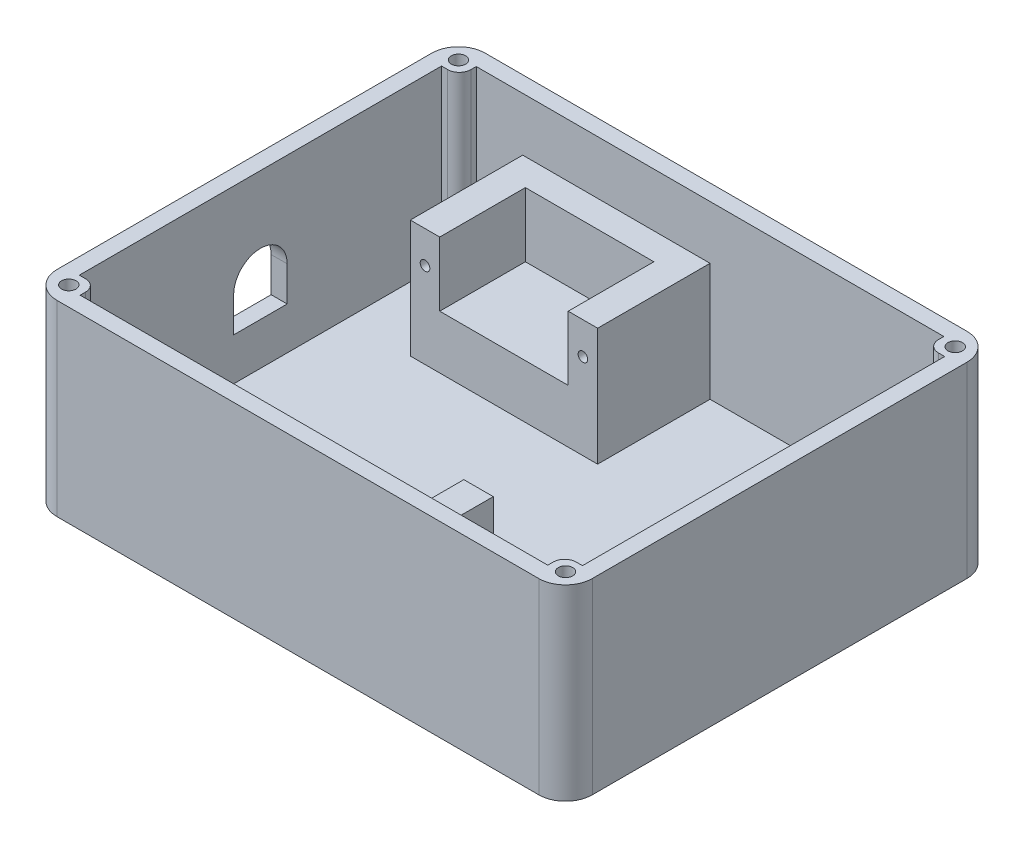
SolidWorks part; units mm, degrees
ref_plane "Front" through (0, 0, 0) normal (0, 0, 1) x (1, 0, 0)
ref_plane "Top" through (0, 0, 0) normal (0, 1, 0) x (1, 0, 0)
ref_plane "Right" through (0, 0, 0) normal (1, 0, 0) x (0, 0, -1)
sketch "草图1" plane through (0, 0, 0) normal (0, 1, 0) x (1, 0, 0)
  line L1 (-45, 40) -> (45, 40)
  line L2 (-50, 35) -> (-50, -35)
  line L3 (-45, -40) -> (45, -40)
  line L4 (50, 35) -> (50, -35)
  line L5 (-50, 40) -> (50, -40) construction
  line L6 (-50, -40) -> (50, 40) construction
  arc A0 (-50, -35) -> (-45, -40) centre (-45, -35) ccw
  arc A1 (45, -40) -> (50, -35) centre (45, -35) ccw
  arc A2 (45, 40) -> (50, 35) centre (45, 35) cw
  arc A3 (-45, 40) -> (-50, 35) centre (-45, 35) ccw
  point P0 (0, 0)
  dimension "D3" = 5
  dimension "D1" = 100
  dimension "D2" = 80
extrude "凸台-拉伸1" add sketch "草图1" along normal blind 35
shell "抽壳2" thickness 3
sketch "草图2" plane through (0, 3, 0) normal (0, 1, 0) x (1, 0, 0)
  line L0 (0, 15.372) -> (0, -17.8847) construction
  line L2 (45, 37) -> (-45, 37) construction
  line L3 (-18.0497, 0) -> (18.0623, 0) construction
  line L4 (47, 33.835) -> (47, 35)
  line L5 (45.8439, 33.835) -> (47, 33.835)
  line L6 (43.6788, 36) -> (43.6788, 37)
  line L7 (-43.6788, 36) -> (-43.6788, 37)
  line L8 (-45.8439, 33.835) -> (-47, 33.835)
  line L9 (-47, 35) -> (-47, -35) construction
  line L10 (-47, 33.835) -> (-47, 35)
  line L11 (-43.6788, 37) -> (-45, 37)
  line L12 (43.6788, 37) -> (45, 37)
  line L13 (43.6788, -37) -> (45, -37)
  line L14 (43.6788, -36) -> (43.6788, -37)
  line L15 (45.8439, -33.835) -> (47, -33.835)
  line L16 (47, -33.835) -> (47, -35)
  line L17 (-47, -33.835) -> (-47, -35)
  line L18 (-45.8439, -33.835) -> (-47, -33.835)
  line L19 (-43.6788, -36) -> (-43.6788, -37)
  line L20 (-43.6788, -37) -> (-45, -37)
  arc A0 (-45.8439, 33.835) -> (-43.6788, 36) centre (-45.8439, 36) ccw
  arc A1 (-45, 37) -> (-47, 35) centre (-45, 35) ccw construction
  arc A2 (-45, 37) -> (-47, 35) centre (-45, 35) ccw
  arc A3 (45, 37) -> (47, 35) centre (45, 35) cw
  arc A4 (45.8439, 33.835) -> (43.6788, 36) centre (45.8439, 36) cw
  arc A5 (45.8439, -33.835) -> (43.6788, -36) centre (45.8439, -36) ccw
  arc A6 (45, -37) -> (47, -35) centre (45, -35) ccw
  arc A7 (-45, -37) -> (-47, -35) centre (-45, -35) cw
  arc A8 (-45.8439, -33.835) -> (-43.6788, -36) centre (-45.8439, -36) cw
  dimension "D1" = 1
extrude "凸台-拉伸3" add sketch "草图2" along normal blind 32
sketch "草图3" plane through (0, 35, 0) normal (0, 1, 0) x (1, 0, 0)
  line L0 (43.6788, 37) -> (-43.6788, 37) construction
  line L1 (-47, 33.835) -> (-47, -33.835) construction
  line L2 (0, 14.6286) -> (0, -16.7471) construction
  line L3 (-18.4739, 0) -> (20.7457, 0) construction
  circle A0 centre (-46.4, 36.4) radius 1.35
  circle A1 centre (46.4, 36.4) radius 1.35
  circle A2 centre (46.4, -36.4) radius 1.35
  circle A3 centre (-46.4, -36.4) radius 1.35
  dimension "D1" = 0.6
  dimension "D3" = 2.7
  dimension "D2" = 0.6
extrude "切除-拉伸1" cut sketch "草图3" against normal blind 4
sketch "草图6" plane through (-50, 0, 0) normal (-1, 0, 0) x (0, 0, 1)
  line L2 (-5, 17.419) -> (-5, 10.919)
  line L3 (-5, 10.919) -> (5, 10.919)
  line L4 (5, 17.419) -> (5, 10.919)
  arc A0 (5, 17.419) -> (-5, 17.419) centre (0, 17.419) ccw
  dimension "D1" = 10
  dimension "D2" = 6.5
extrude "切除-拉伸4" cut sketch "草图6" against normal blind 3
sketch "草图7" plane through (0, 3, 0) normal (0, 1, 0) x (1, 0, 0)
  line L0 (43.6788, 37) -> (-43.6788, 37) construction
  line L2 (0, 37) -> (0, 16)
  line L7 (0, 16) -> (-35, 16)
  line L8 (0, 16) -> (0, 37)
  line L9 (0, 37) -> (-35, 37)
  line L10 (-35, 16) -> (-35, 37)
  line L15 (12, -37) -> (47, -37)
  line L16 (12, -37) -> (12, -21)
  line L17 (12, -21) -> (47, -21)
  line L18 (47, -37) -> (47, -21)
  line L19 (47, -33.835) -> (47, 33.835) construction
  line M7 (-43.6788, -37) -> (43.6788, -37)
  line M15 (43.6788, 37) -> (-43.6788, 37)
  dimension "D1" = 16
  dimension "D2" = 35
  dimension "D3" = 0
  dimension "D4" = 21
  dimension "D5" = 35
extrude "凸台-拉伸4" add sketch "草图7" along normal blind 22 contours L10 L7 L2 M15 | L18 L17 L16 M7
sketch "草图8" plane through (0, 25, 0) normal (0, 1, 0) x (1, 0, 0)
  line L5 (12, -37) -> (-43.6788, -37) construction
  line L6 (17.5, -21) -> (41.5, -21)
  line L12 (0, 16) -> (-35, 16) construction
  line L13 (-5.5, 16) -> (-29.5, 16)
  line L14 (-5.5, 16) -> (-5.5, 32)
  line L15 (-5.5, 32) -> (-29.5, 32)
  line L16 (-29.5, 16) -> (-29.5, 32)
  line L17 (0, 37) -> (-35, 37) construction
  line L19 (17.5, -21) -> (17.5, -37)
  line L20 (17.5, -37) -> (41.5, -37)
  line L21 (41.5, -21) -> (41.5, -37)
  line L22 (17.5, -21) -> (41.5, -37) construction
  line L23 (17.5, -37) -> (41.5, -21) construction
  line L24 (12, -21) -> (47, -21) construction
  line L26 (12, -21) -> (47, -21) construction
  point P0 (23, 8)
  point P1 (29.5, -29)
  point P7 (-16.9656, 27)
  point P15 (29.5, -21)
  point P16 (-17.5, 37)
  point P18 (29.5, -21)
  point P20 (29.5, -21)
  point P22 (-17.5, 32)
  dimension "D1" = 24
  dimension "D2" = 24
  dimension "D3" = 16
  dimension "D4" = 16
extrude "切除-拉伸5" cut sketch "草图8" against normal blind 12
sketch "草图9" plane through (0, 0, -16) normal (0, 0, 1) x (1, 0, 0)
  line L1 (-29.5, 25) -> (-35, 25) construction
  line L2 (-17.5, 13) -> (-17.5, 18.7482) construction
  line L3 (-29.5, 13) -> (-5.5, 13) construction
  line L4 (0, 25) -> (-5.5, 25) construction
  circle A0 centre (-2.75, 19) radius 0.9
  circle A2 centre (-32.25, 19) radius 0.9
  point P2 (-2.75, 25)
  point P5 (-32.25, 25)
  dimension "D1" = 6
  dimension "D2" = 1.8
extrude "切除-拉伸6" cut sketch "草图9" against normal blind 5
sketch "草图10" plane through (0, 0, 21) normal (0, 0, -1) x (-1, 0, 0)
  line L0 (-29.5, 26.6565) -> (-29.5, 4.0922) construction
  line L1 (-41.5, 13) -> (-41.5, 25) construction
  circle A0 centre (-44, 19) radius 0.9
  circle A4 centre (-15, 19) radius 0.9
  dimension "D1" = 2.5
  dimension "D2" = 1.8
extrude "切除-拉伸7" cut sketch "草图10" against normal blind 4
